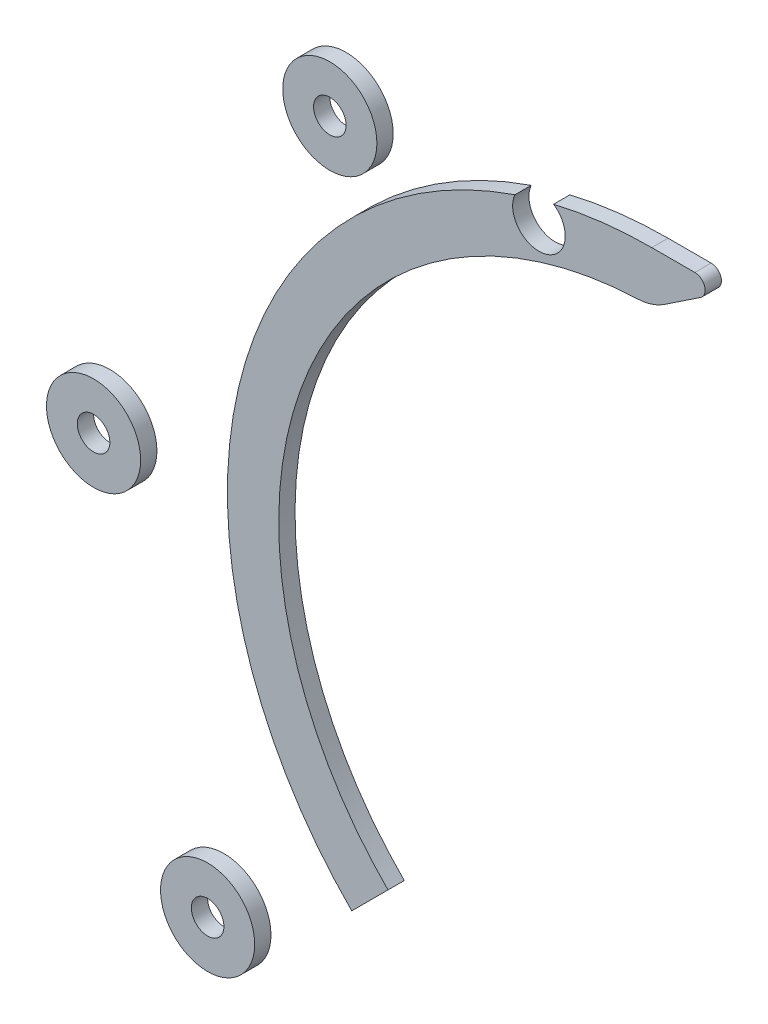
SolidWorks part; units mm, degrees
ref_plane "Front Plane" through (0, 0, 0) normal (0, 0, 1) x (1, 0, 0)
ref_plane "Top Plane" through (0, 0, 0) normal (0, 1, 0) x (1, 0, 0)
ref_plane "Right Plane" through (0, 0, 0) normal (1, 0, 0) x (0, 0, -1)
sketch "Sketch1" plane through (0, 0, 0) normal (0, 0, 1) x (1, 0, 0)
  line L1 (0, 72.7242) -> (0, 82.7242)
  line L2 (0, 82.7242) -> (-62.7633, 82.7242)
  line L3 (-95.3374, -76.366) -> (-117.3524, -6.4437)
  line L4 (-111.5654, -82.6057) -> (-56.3997, -83.0034) construction
  line L5 (-51.4238, -51.4238) -> (-80.0983, -80.0983)
  line L6 (-76.6442, 68.2738) -> (-116.6786, 1.7263)
  line L7 (0, 0) -> (-80.0983, -80.0983) construction
  line L9 (-117.9938, -3.279) -> (-118.5148, -75.5555) construction
  line L10 (-73.8989, 44.2974) -> (-115.014, 3.7708) construction
  arc A0 (0, 72.7242) -> (-51.4238, -51.4238) centre (0, 0) ccw
  arc A3 (0, 82.7242) -> (-58.4948, -58.4948) centre (0, 0) ccw
  circle A4 centre (0, 0) radius 72.7242 construction
  circle A5 centre (0, 0) radius 82.7242 construction
  circle A6 centre (-62.7633, 73.5492) radius 3.175
  circle A8 centre (-62.7633, 73.5492) radius 9.175
  circle A9 centre (-86.586, -73.6106) radius 3.175
  circle A10 centre (-86.586, -73.6106) radius 9.175
  circle A11 centre (-108.8166, -3.0034) radius 3.175
  circle A12 centre (-108.8166, -3.0034) radius 9.175
  arc A13 (-63.9504, 73.0536) -> (-59.2107, 74.9364) centre (-61.5806, 73.995) ccw construction
  arc A14 (-63.9504, 73.0536) -> (-59.2107, 74.9364) centre (-61.5806, 73.995) ccw
  point P23 (-86.586, -73.6106)
  point P29 (-86.586, -73.6106)
  point P33 (-102.6946, 124.8945)
  point P34 (-101.0787, -94.4627)
  point P35 (0, 0)
  point P36 (0, 0)
  point P37 (0, 0)
  point P38 (0, 0)
  point P39 (-62.5124, 73.5492)
  point P40 (-62.7633, 72.8987)
  point P44 (-62.7633, 73.5492)
  point P45 (-86.586, -73.6106)
  dimension "D1" = 10
  dimension "D2" = 6.35
  dimension "D3" = 6
  dimension "D4" = 72.7242
  dimension "D5" = 18.35
  dimension "D7" = 6.35
  dimension "D8" = 18.35
  dimension "D6" = 135
extrude "Boss-Extrude1" add sketch "Sketch1" against normal blind 3.175
sketch "Sketch3" plane through (0, 0, -3.175) normal (0, 0, -1) x (-1, 0, 0)
  line L0 (0, 72.7242) -> (0, 82.7242) construction
  line L3 (0, 82.7242) -> (77.9085, 82.7242) construction
  circle A0 centre (22, 76.2242) radius 5.125
  point P2 (21.8596, 75.8588)
  point P7 (21.5953, 82.7242)
  point P8 (5.2923, 82.7242)
  dimension "D1" = 10.25
  dimension "D2" = 22
  dimension "D3" = 6.5
extrude "Cut-Extrude1" cut sketch "Sketch3" against normal blind 10
sketch "Sketch4" plane through (0, 0, 0) normal (0, 0, 1) x (1, 0, 0)
  line L0 (0, 82.7242) -> (15, 82.7242)
  line L1 (15, 82.7242) -> (0, 72.7242)
  line L2 (0, 72.7242) -> (0, 82.7242)
  dimension "D1" = 15
extrude "Boss-Extrude2" add sketch "Sketch4" against normal up to surface (3.175 mm away) up to face at (-83.411, -73.6106, -3.175)
fillet "Fillet1" radius 10 1 edges at (0, 72.7242, -1.5875)
fillet "Fillet2" radius 2 1 edges at (15, 82.7242, -1.5875)
